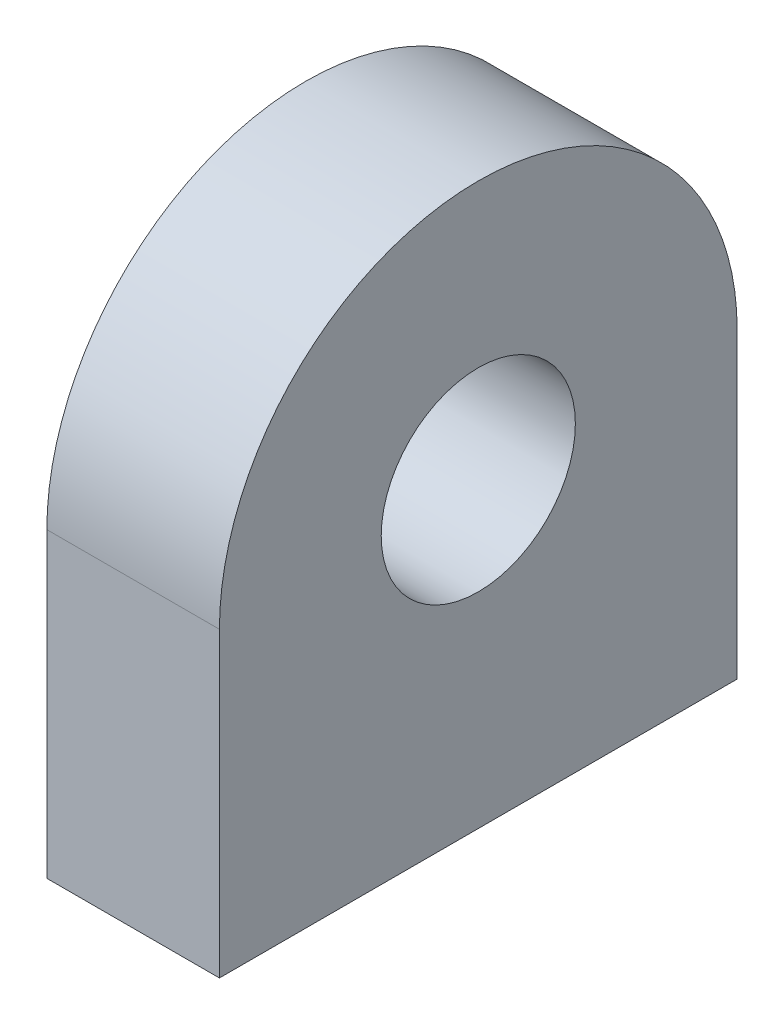
SolidWorks part; units mm, degrees
ref_plane "Front Plane" through (0, 0, 0) normal (0, 0, 1) x (1, 0, 0)
ref_plane "Top Plane" through (0, 0, 0) normal (0, 1, 0) x (1, 0, 0)
ref_plane "Right Plane" through (0, 0, 0) normal (1, 0, 0) x (0, 0, -1)
sketch "Sketch1" plane through (0, 0, 0) normal (1, 0, 0) x (0, 0, -1)
  line L0 (-38.1, 0) -> (38.1, 0)
  line L1 (38.1, 0) -> (38.1, 44.45)
  line L2 (-38.1, 0) -> (-38.1, 44.45)
  line L3 (-38.1, 44.45) -> (38.1, 44.45) construction
  arc A0 (-38.1, 44.45) -> (38.1, 44.45) centre (0, 44.45) cw
  circle A1 centre (0, 44.45) radius 14.2875
  dimension "D1" = 38.1
  dimension "D2" = 28.575
  dimension "D3" = 44.45
extrude "Boss-Extrude1" add sketch "Sketch1" along normal mid plane 25.4
sketch "Sketch2" plane through (0, 0, 0) normal (0, -1, 0) x (1, 0, 0)
  line L0 (0, 38.1) -> (0, -37.7498) construction
  line L1 (12.7, 38.1) -> (-12.7, 38.1) construction
  line L2 (-12.7, 0) -> (12.7, 0) construction
  line L3 (-12.7, 38.1) -> (-12.7, -38.1) construction
  line L4 (12.7, 38.1) -> (12.7, -38.1) construction
